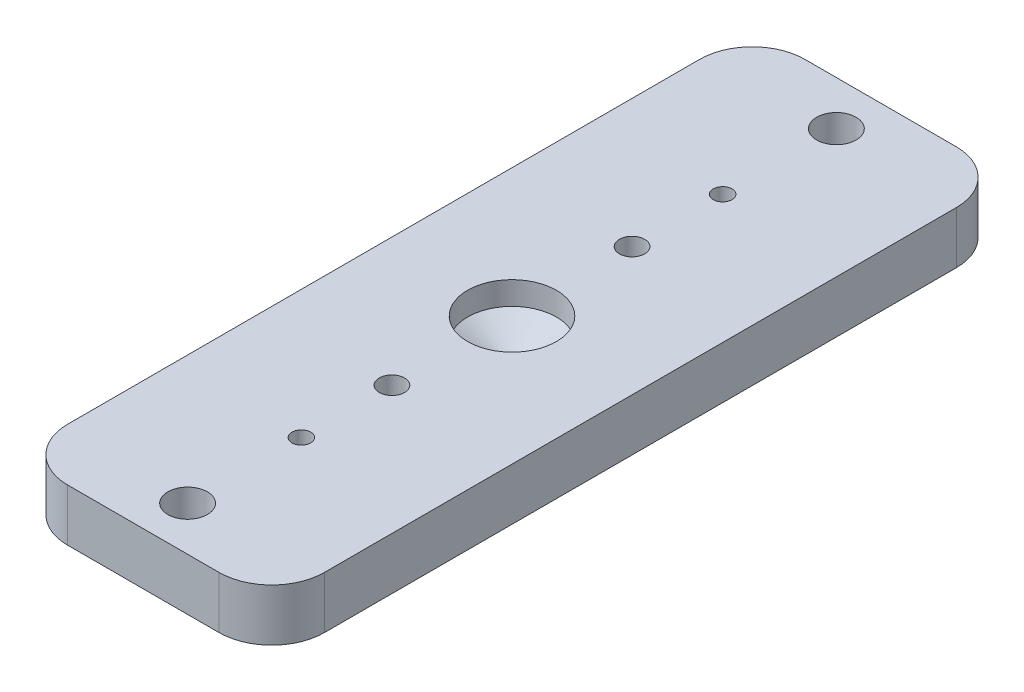
SolidWorks part; units mm, degrees
ref_plane "Front Plane" through (0, 0, 0) normal (0, 0, 1) x (1, 0, 0)
ref_plane "Top Plane" through (0, 0, 0) normal (0, 1, 0) x (1, 0, 0)
ref_plane "Right Plane" through (0, 0, 0) normal (1, 0, 0) x (0, 0, -1)
sketch "Sketch1" plane through (0, 0, 0) normal (0, 1, 0) x (1, 0, 0)
  line L0 (-15.4781, -44.45) -> (-15.4781, 44.45)
  line L1 (15.4781, 44.45) -> (15.4781, -44.45)
  line L2 (-15.4781, 0) -> (15.4781, 0) construction
  line L3 (0, 41.275) -> (0, -41.275) construction
  line L4 (-15.4781, 44.45) -> (15.4781, 44.45)
  line L5 (-15.4781, -44.45) -> (15.4781, -44.45)
  dimension "D2" = 30.9562
  dimension "D1" = 88.9
extrude "Boss-Extrude1" add sketch "Sketch1" along normal blind 4.7625
fillet "Fillet1" radius 6.35 4 edges at (15.4781, 2.3813, -44.45) (-15.4781, 2.3813, -44.45) (15.4781, 2.3813, 44.45) (-15.4781, 2.3813, 44.45)
sketch "Sketch6" plane through (0, 0, 0) normal (0, -1, 0) x (1, 0, 0)
  line L0 (0, 0) -> (-28.2073, 0) construction
  line L1 (-9.1281, 44.45) -> (9.1281, 44.45) construction
  circle A0 centre (0, 14.478) radius 1.524
  circle A1 centre (0, -14.478) radius 1.524
  point P9 (0, 44.45)
  dimension "D1" = 3.048
  dimension "D2" = 14.478
extrude "Cut-Extrude1" cut sketch "Sketch6" against normal through all
sketch "Sketch7" plane through (0, 0, 0) normal (0, -1, 0) x (1, 0, 0)
  line L1 (9.1281, -44.45) -> (-9.1281, -44.45) construction
  line L2 (0, 0) -> (-19.1679, 0) construction
  circle A0 centre (0, -39.116) radius 2.3812
  circle A1 centre (0, 39.116) radius 2.3812
  dimension "D1" = 4.7625
  dimension "D2" = 5.334
extrude "Cut-Extrude2" cut sketch "Sketch7" against normal through all
sketch "Sketch9" plane through (0, 0, 0) normal (0, -1, 0) x (1, 0, 0)
  line L0 (9.1281, -44.45) -> (-9.1281, -44.45) construction
  line L1 (15.4781, 38.1) -> (15.4781, -38.1) construction
  line L2 (-15.4781, -38.1) -> (-15.4781, 38.1) construction
  line L3 (-9.1281, 44.45) -> (9.1281, 44.45) construction
  line L4 (9.1281, -44.45) -> (-9.1281, -44.45)
  line L5 (15.4781, 38.1) -> (15.4781, -38.1)
  line L6 (-15.4781, -38.1) -> (-15.4781, 38.1)
  line L7 (-9.1281, 44.45) -> (9.1281, 44.45)
  arc A0 (9.1281, -44.45) -> (15.4781, -38.1) centre (9.1281, -38.1) ccw construction
  arc A1 (-15.4781, -38.1) -> (-9.1281, -44.45) centre (-9.1281, -38.1) ccw construction
  arc A2 (15.4781, 38.1) -> (9.1281, 44.45) centre (9.1281, 38.1) ccw construction
  arc A3 (-9.1281, 44.45) -> (-15.4781, 38.1) centre (-9.1281, 38.1) ccw construction
  arc A4 (9.1281, -44.45) -> (15.4781, -38.1) centre (9.1281, -38.1) ccw
  arc A5 (-15.4781, -38.1) -> (-9.1281, -44.45) centre (-9.1281, -38.1) ccw
  arc A6 (15.4781, 38.1) -> (9.1281, 44.45) centre (9.1281, 38.1) ccw
  arc A7 (-9.1281, 44.45) -> (-15.4781, 38.1) centre (-9.1281, 38.1) ccw
extrude "Boss-Extrude3" add sketch "Sketch9" along normal blind 1.524
hole_wizard "#4-40 Tapped Hole1" positions "Sketch5" profile "Sketch4" tap size "#4-40" standard "Ansi Inch" end condition through all
sketch "Sketch5" plane through (0, 4.7625, 0) normal (0, 1, 0) x (-1, 0, 0)
  line L0 (0, 0) -> (16.1552, 0) construction
  point P0 (0, 25.4)
  point P9 (0, -25.4)
  dimension "D1" = 50.8
sketch "Sketch4" plane through (0, 4.7625, 25.4) normal (1, 0, 0) x (0, 0, 1)
  line L0 (0, 0) -> (0, 6.2865)
  line L1 (0, 6.2865) -> (1.1303, 6.2865)
  line L2 (1.1303, 6.2865) -> (1.1303, 0)
  line L5 (1.1303, 0) -> (0, 0)
  line L11 (0, -6.35) -> (0, 107.95) construction
  dimension "Thread Major Dia." = 2.2606
  dimension "Thru Tap Drill Depth" = 6.2865
sketch "Sketch10" plane through (0, 0, 0) normal (0, 1, 0) x (1, 0, 0)
  circle A0 centre (0, -14.478) radius 1.524 construction
  circle A1 centre (0, 14.478) radius 1.524 construction
  circle A2 centre (0, -14.478) radius 1.524
  circle A3 centre (0, 14.478) radius 1.524
extrude "Cut-Extrude3" cut sketch "Sketch10" against normal through all
sketch "Sketch11" plane through (0, -1.524, 0) normal (0, -1, 0) x (1, 0, 0)
  line L0 (0, 0) -> (-8.2063, 0) construction
  circle A0 centre (0, -14.478) radius 3.175
  circle A1 centre (0, 14.478) radius 3.175
  dimension "D1" = 6.35
extrude "Cut-Extrude4" cut sketch "Sketch11" against normal blind 3.302
hole_wizard "1/2-13 Tapped Hole2" positions "Sketch15" profile "Sketch14" tap size "1/2-13" standard "Ansi Inch"
sketch "Sketch15" plane through (0, 4.7625, 0) normal (0, 1, 0) x (-1, 0, 0)
  point P0 (0, 0)
sketch "Sketch14" plane through (0, 4.7625, 0) normal (1, 0, 0) x (0, 0, 1)
  line L0 (0, 0) -> (0, 6.0135)
  line L1 (0, 6.0135) -> (5.3581, 2.794)
  line L2 (5.3581, 2.794) -> (5.3581, 0)
  line L5 (5.3581, 0) -> (0, 0)
  line L10 (0, 6.0135) -> (-5.3581, 2.794) construction
  line L11 (0, -6.35) -> (0, 107.95) construction
  dimension "Tap Drill Dia." = 10.7163
  dimension "Tap Drill Depth" = 2.794
  dimension "Drill Angle" = 118
cosmetic thread "Hole Thread2" parameters "D1"=2.794, "D2"=12.7
